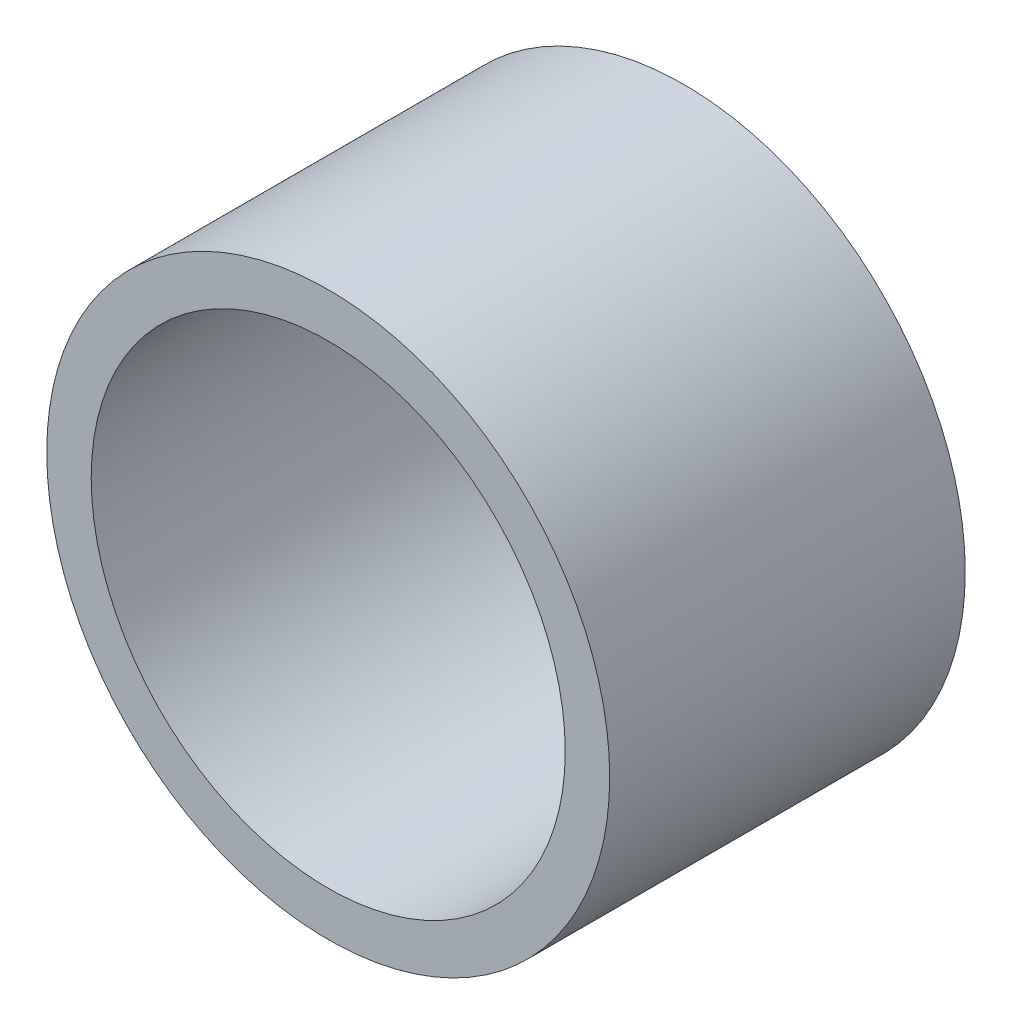
SolidWorks part; units mm, degrees
ref_plane "Front Plane" through (0, 0, 0) normal (0, 0, 1) x (1, 0, 0)
ref_plane "Top Plane" through (0, 0, 0) normal (0, 1, 0) x (1, 0, 0)
ref_plane "Right Plane" through (0, 0, 0) normal (1, 0, 0) x (0, 0, -1)
sketch "Sketch1" plane through (0, 0, 0) normal (0, 0, 1) x (1, 0, 0)
  circle A0 centre (0, 0) radius 8
  circle A1 centre (0, 0) radius 9.5
  dimension "D1" = 19
  dimension "D2" = 16
extrude "Boss-Extrude1" add sketch "Sketch1" along normal blind 12
